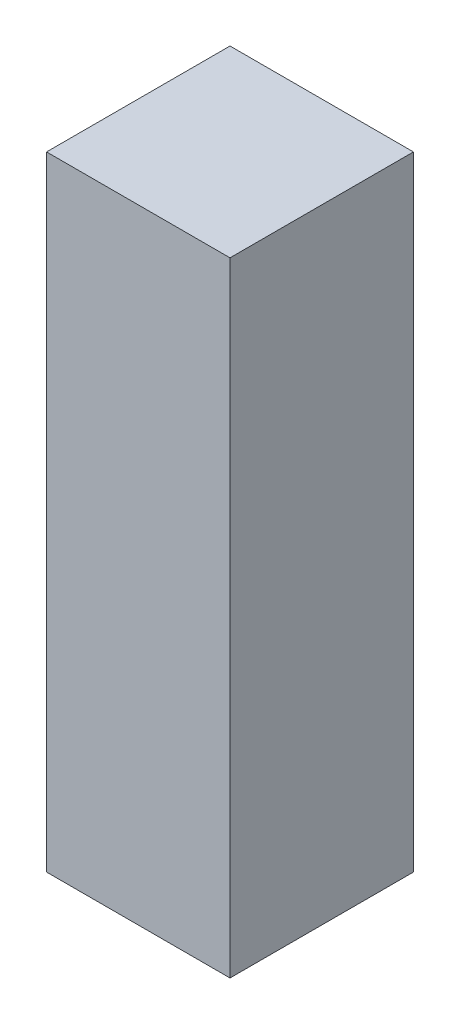
SolidWorks part; units mm, degrees
ref_plane "Front Plane" through (0, 0, 0) normal (0, 0, 1) x (1, 0, 0)
ref_plane "Top Plane" through (0, 0, 0) normal (0, 1, 0) x (1, 0, 0)
ref_plane "Right Plane" through (0, 0, 0) normal (1, 0, 0) x (0, 0, -1)
sketch "Sketch1" plane through (0, 0, 0) normal (0, 1, 0) x (1, 0, 0)
  line L1 (-0.25, -0.25) -> (0.25, -0.25)
  line L2 (-0.25, -0.25) -> (-0.25, 0.25)
  line L3 (-0.25, 0.25) -> (0.25, 0.25)
  line L4 (0.25, -0.25) -> (0.25, 0.25)
  line L5 (-0.25, -0.25) -> (0.25, 0.25) construction
  line L6 (-0.25, 0.25) -> (0.25, -0.25) construction
  point P0 (0, 0)
  dimension "D1" = 0.5
extrude "Boss-Extrude1" add sketch "Sketch1" along normal mid plane 1.7
